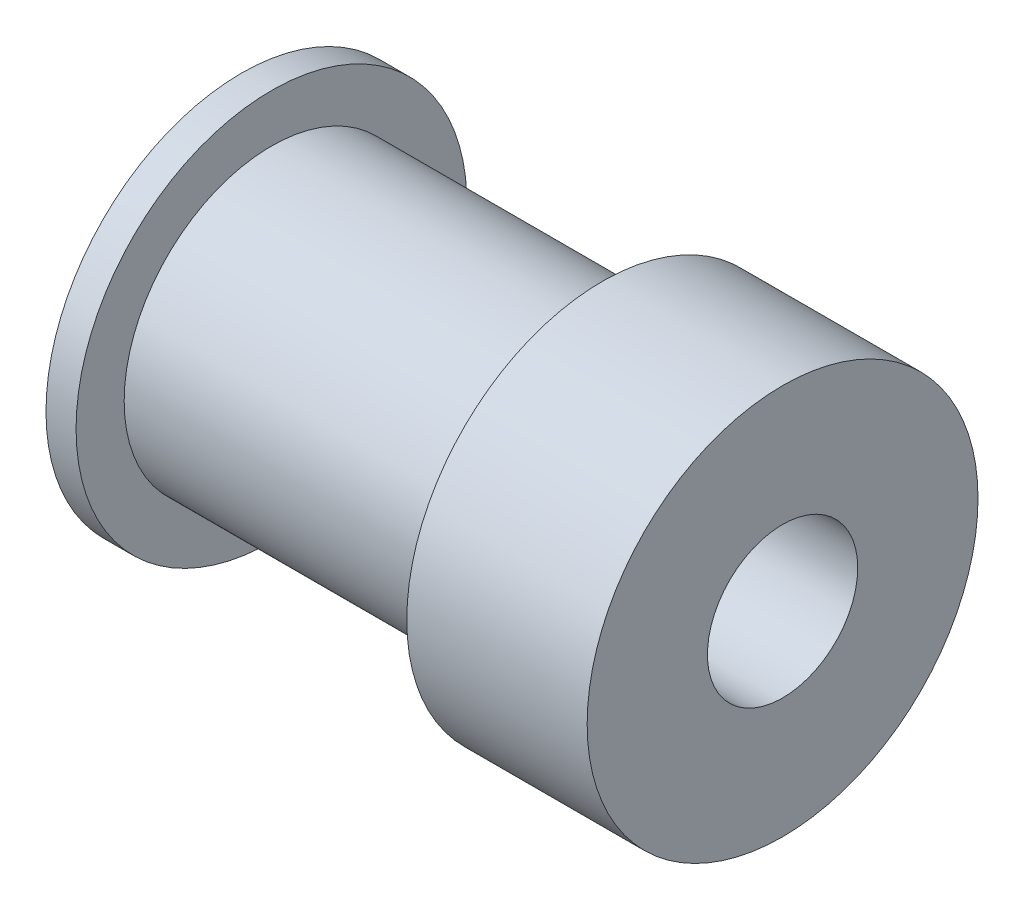
SolidWorks part; units mm, degrees
ref_plane "Front Plane" through (0, 0, 0) normal (0, 0, 1) x (1, 0, 0)
ref_plane "Top Plane" through (0, 0, 0) normal (0, 1, 0) x (1, 0, 0)
ref_plane "Right Plane" through (0, 0, 0) normal (1, 0, 0) x (0, 0, -1)
sketch "Sketch1" plane through (0, 0, 0) normal (1, 0, 0) x (0, 0, -1)
  circle A0 centre (0, 0) radius 2.5
  circle A1 centre (0, 0) radius 6.5
  dimension "D1" = 5
  dimension "D2" = 13
extrude "Boss-Extrude1" add sketch "Sketch1" along normal blind 18
ref_plane "Plane1" through (1, 0, 0) normal (-1, 0, 0) x (0, 0, 1)
sketch "Sketch2" plane through (1, 0, 0) normal (-1, 0, 0) x (0, 0, 1)
  circle A0 centre (0, 0) radius 4.9
  circle A1 centre (0, 0) radius 6.5 construction
  circle A2 centre (0, 0) radius 6.5
  dimension "D1" = 9.8
extrude "Cut-Extrude1" cut sketch "Sketch2" against normal blind 11
